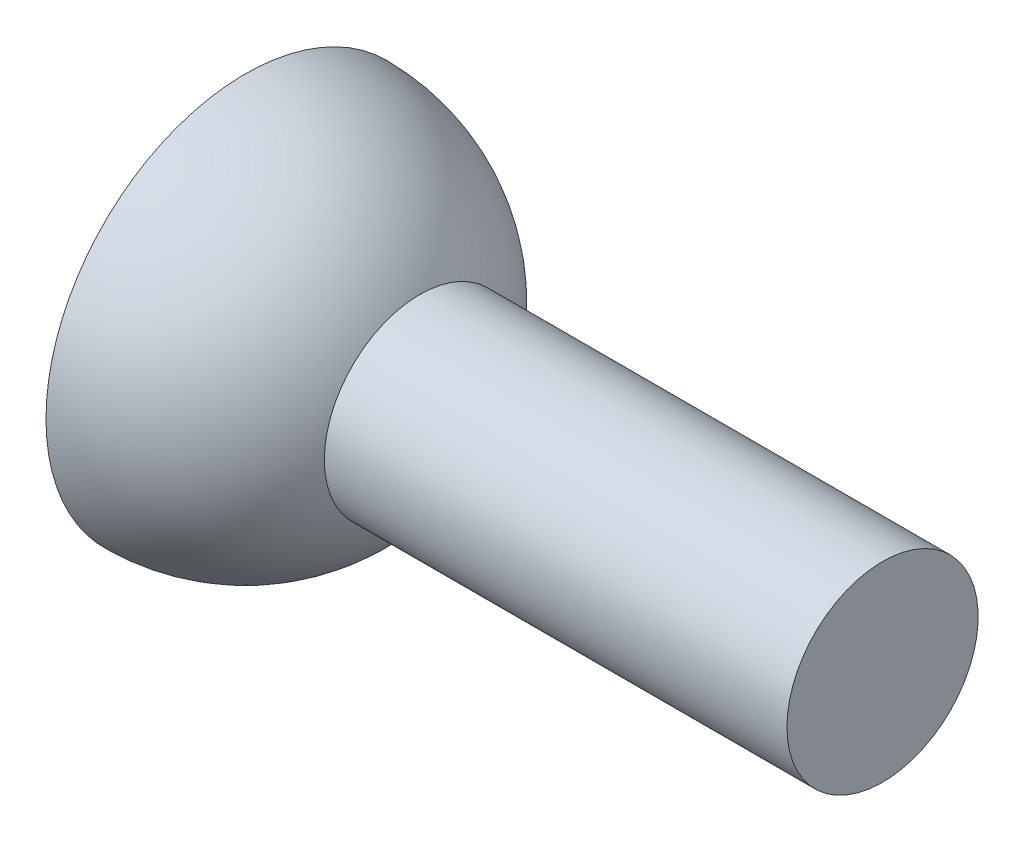
SolidWorks part; units mm, degrees
ref_plane "Front Plane" through (0, 0, 0) normal (0, 0, 1) x (1, 0, 0)
ref_plane "Top Plane" through (0, 0, 0) normal (0, 1, 0) x (1, 0, 0)
ref_plane "Right Plane" through (0, 0, 0) normal (1, 0, 0) x (0, 0, -1)
sketch "Sketch2" plane through (0, 0, 0) normal (0, 1, 0) x (1, 0, 0)
  line L0 (0, 25) -> (0, 0)
  line L1 (0, 0) -> (25, 0)
  arc A0 (25, 0) -> (0, 25) centre (0, 0) ccw
  dimension "D1" = 50
revolve "Revolve1" add sketch "Sketch2" angle 360 about L1
shell "Shell1" thickness 5
sketch "Sketch3" plane through (0, 0, 0) normal (0, 0, 1) x (1, 0, 0)
  line L0 (20, 0) -> (20, 12)
  line L1 (20, 12) -> (80, 12)
  line L2 (80, 12) -> (80, 0)
  line L3 (20, 0) -> (80, 0)
  dimension "D1" = 12
  dimension "D2" = 60
  dimension "D3" = 20
revolve "Revolve3" add sketch "Sketch3" angle 360 about L3
